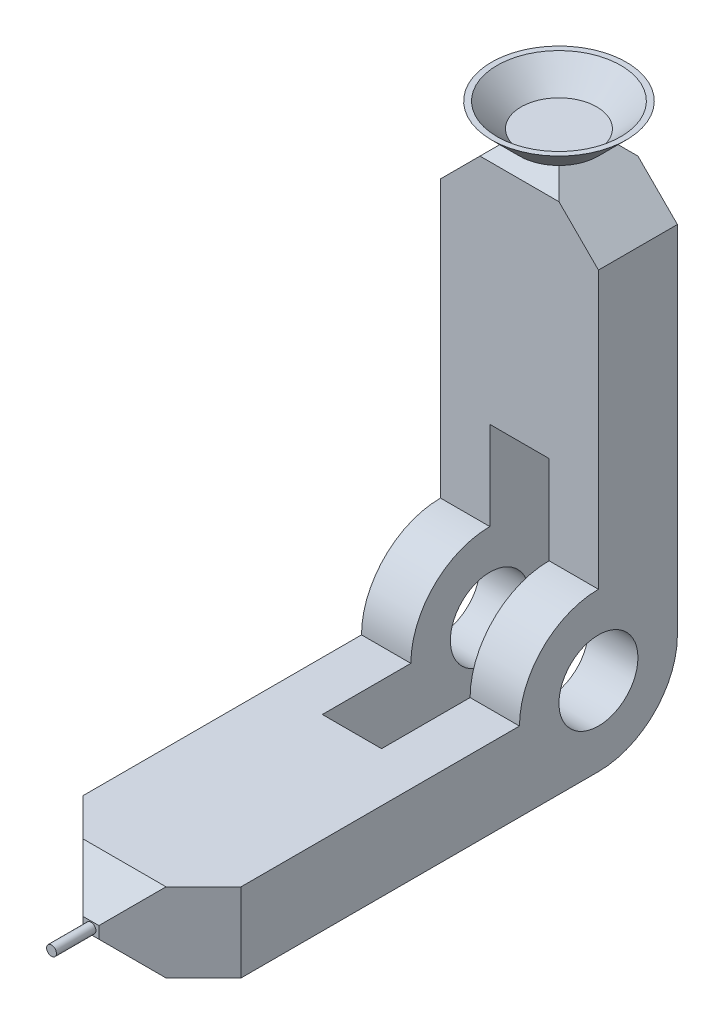
SolidWorks part; units mm, degrees
ref_plane "Front Plane" through (0, 0, 0) normal (0, 0, 1) x (1, 0, 0)
ref_plane "Top Plane" through (0, 0, 0) normal (0, 1, 0) x (1, 0, 0)
ref_plane "Right Plane" through (0, 0, 0) normal (1, 0, 0) x (0, 0, -1)
sketch "sketch1_tool_tip" plane through (0, 0, 0) normal (1, 0, 0) x (0, 0, -1)
  line L0 (-100, 0) -> (-108.5, -8.5)
  line L1 (-100, -20) -> (-108.5, -11.5)
  line L2 (0, 100) -> (0, 20)
  line L3 (-100, 0) -> (-20, 0)
  line L4 (0, -20) -> (-100, -20)
  line L5 (20, 0) -> (20, 100)
  line L6 (-108.5, -11.5) -> (-108.5, -8.5)
  line L7 (0, 100) -> (5, 105)
  line L8 (5, 105) -> (15, 105)
  line L9 (15, 105) -> (20, 100)
  circle A0 centre (0, 0) radius 10
  arc A1 (0, -20) -> (20, 0) centre (0, 0) ccw
  arc A2 (0, 20) -> (-20, 0) centre (0, 0) ccw
  dimension "D1" = 20
  dimension "D3" = 20
  dimension "D6" = 135
  dimension "D2" = 20
  dimension "D4" = 20
  dimension "D5" = 100
  dimension "D7" = 135
  dimension "D8" = 3
  dimension "D9" = 135
  dimension "D10" = 135
  dimension "D11" = 10
extrude "Boss-Extrude1" add sketch "sketch1_tool_tip" along normal mid plane 40
chamfer "Chamfer1" distance 18 angle 45 2 edges at (-20, -10, 108.5) (20, -10, 108.5)
sketch "sketch2_tool_tip" plane through (0, 0, 0) normal (1, 0, 0) x (0, 0, -1)
  line L1 (-42.42, -20) -> (0, -20)
  line L2 (20, 0) -> (20, 42.42)
  line L4 (-20, 0) -> (-42.42, 0)
  line L5 (-20, 0) -> (-90.5, 0) construction
  line L6 (-90.5, -20) -> (0, -20) construction
  line L7 (0, 20) -> (0, 42.42)
  line L8 (0, 100) -> (0, 20) construction
  line L9 (20, 0) -> (20, 100) construction
  line L10 (0, 42.42) -> (20, 42.42)
  line L11 (-42.42, 0) -> (-42.42, -20)
  arc A1 (0, -20) -> (20, 0) centre (0, 0) ccw
  arc A2 (0, 20) -> (-20, 0) centre (0, 0) ccw
  dimension "D1" = 20
  dimension "D2" = 42.42
extrude "Cut-Extrude1" cut sketch "sketch2_tool_tip" against normal mid plane 15
sketch "sketch3_tool_tip" plane through (0, 0, 108.5) normal (0, 0, 1) x (1, 0, 0)
  line L0 (0, -8.5) -> (0, -11.5) construction
  line L1 (2, -8.5) -> (-2, -8.5) construction
  line L2 (2, -11.5) -> (-2, -11.5) construction
  circle A0 centre (0, -10) radius 1.25
  dimension "D1" = 2.5
extrude "Boss-Extrude2" add sketch "sketch3_tool_tip" along normal blind 10
chamfer "Chamfer2" distance 15 angle 45 2 edges at (-20, 105, -10) (20, 105, -10)
ref_point "p1_ref_gripper"
ref_point "p2_ref_gripper"
ref_axis "axis_ref_gripper" through (0, 105, -10) along (0, -1, 0)
ref_plane "plane_ref_gripper" through (0, 0, -10) normal (0, 0, -1) x (-1, 0, 0)
ref_point "point_ref_gripper"
sketch "sketch4_tool_tip" plane through (0, 0, -10) normal (0, 0, -1) x (-1, 0, 0)
  line L0 (0, 105) -> (10, 105)
  line L1 (10, 105) -> (17.0711, 112.0711)
  line L2 (17.0711, 112.0711) -> (15.6569, 112.0711)
  line L3 (15.6569, 112.0711) -> (9.5858, 106)
  line L4 (9.5858, 106) -> (0, 106)
  line L5 (0, 106) -> (0, 105)
  line L6 (15.6569, 112.0711) -> (16.364, 111.364) construction
  dimension "D1" = 135
  dimension "D2" = 10
  dimension "D3" = 1
  dimension "D4" = 10
revolve "Revolve1" add sketch "sketch4_tool_tip" angle 360 about axis through (0, 105, -10) along (0, -1, 0)
